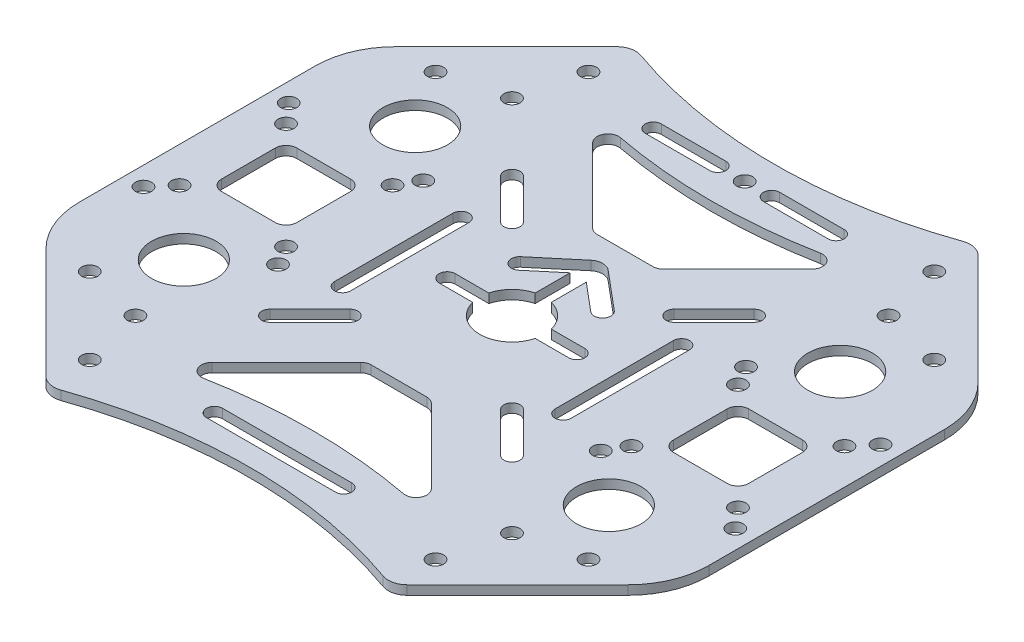
SolidWorks part; units mm, degrees
ref_plane "前基準面" through (0, 0, 0) normal (0, 0, 1) x (1, 0, 0)
ref_plane "上基準面" through (0, 0, 0) normal (0, 1, 0) x (1, 0, 0)
ref_plane "右基準面" through (0, 0, 0) normal (1, 0, 0) x (0, 0, -1)
sketch "草圖1" plane through (0, 0, 0) normal (0, 1, 0) x (1, 0, 0)
  line L0 (-88.3224, -92.0235) -> (-10.6127, -92.0235) construction
  line L1 (-96.5414, 45.9038) -> (-96.5414, -104.0962) construction
  line L2 (0, 5.7817) -> (0, -5.7817) construction
  line L3 (-13.0005, 0) -> (13.0005, 0) construction
  line L4 (-14.25, 25) -> (14.25, 25) construction
  line L5 (-14.25, 26.5) -> (14.25, 26.5)
  line L6 (-14.25, 23.5) -> (14.25, 23.5)
  line L7 (-14.25, -25) -> (14.25, -25) construction
  line L8 (-14.25, -26.5) -> (14.25, -26.5)
  line L9 (-14.25, -23.5) -> (14.25, -23.5)
  line L10 (-47.2341, 47.2341) -> (47.2341, -47.2341) construction
  line L11 (47.2341, 47.2341) -> (-47.2341, -47.2341) construction
  line L12 (-22.5, 22.5) -> (-15.0754, 15.0754) construction
  line L13 (-21.4393, 23.5607) -> (-14.0147, 16.136)
  line L14 (-23.5607, 21.4393) -> (-16.136, 14.0147)
  line L15 (22.5, 22.5) -> (15.0754, 15.0754) construction
  line L16 (21.4393, 23.5607) -> (14.0147, 16.136)
  line L17 (23.5607, 21.4393) -> (16.136, 14.0147)
  line L18 (22.5, -22.5) -> (15.0754, -15.0754) construction
  line L19 (21.4393, -23.5607) -> (14.0147, -16.136)
  line L20 (23.5607, -21.4393) -> (16.136, -14.0147)
  line L21 (-22.5, -22.5) -> (-15.0754, -15.0754) construction
  line L22 (-21.4393, -23.5607) -> (-14.0147, -16.136)
  line L23 (-23.5607, -21.4393) -> (-16.136, -14.0147)
  line L24 (-33.25, 22.4) -> (-33.25, -22.4) construction
  line L25 (-31.75, 22.4) -> (-31.75, -22.4)
  line L26 (-34.75, 22.4) -> (-34.75, -22.4)
  line L27 (-41.25, 23.25) -> (-41.25, -23.25) construction
  line L28 (-39.75, 23.25) -> (-39.75, -23.25)
  line L29 (-42.75, 23.25) -> (-42.75, -23.25)
  line L30 (-50.25, 25.2) -> (-50.25, -25.2) construction
  line L31 (-48.75, 25.2) -> (-48.75, -25.2)
  line L32 (-51.75, 25.2) -> (-51.75, -25.2)
  line L33 (50.25, 25.2) -> (50.25, -25.2) construction
  line L34 (48.75, 25.2) -> (48.75, -25.2)
  line L35 (51.75, 25.2) -> (51.75, -25.2)
  line L36 (41.25, 23.25) -> (41.25, -23.25) construction
  line L37 (39.75, 23.25) -> (39.75, -23.25)
  line L38 (42.75, 23.25) -> (42.75, -23.25)
  line L39 (33.25, 22.4) -> (33.25, -22.4) construction
  line L40 (31.75, 22.4) -> (31.75, -22.4)
  line L41 (34.75, 22.4) -> (34.75, -22.4)
  line L42 (-26, 14.3) -> (-26, -14.3) construction
  line L43 (-24.5, 14.3) -> (-24.5, -14.3)
  line L44 (-27.5, 14.3) -> (-27.5, -14.3)
  line L45 (-1.5, 5.8095) -> (-1.5, 12.3095)
  line L46 (-1.5, 12.3095) -> (-6.7013, 7.9451)
  line L47 (-8.6939, 10.3198) -> (-1.607, 16.2665)
  line L48 (8.6939, 10.3198) -> (1.607, 16.2665)
  line L49 (1.5, 5.8095) -> (1.5, 12.3095)
  line L50 (1.5, 12.3095) -> (6.7013, 7.9451)
  line L51 (26, 14.3) -> (26, -14.3) construction
  line L52 (24.5, 14.3) -> (24.5, -14.3)
  line L53 (27.5, 14.3) -> (27.5, -14.3)
  line L54 (-22.3, -33.3) -> (22.3, -33.3) construction
  line L55 (-22.3, -31.8) -> (22.3, -31.8)
  line L56 (-22.3, -34.8) -> (22.3, -34.8)
  line L57 (-31.9883, -54.6323) -> (-58.5, -28.1206)
  line L58 (-58.5, -28.1206) -> (-58.5, 28.1206)
  line L59 (31.9883, -54.6323) -> (58.5, -28.1206)
  line L60 (58.5, -28.1206) -> (58.5, 28.1206)
  line L61 (-31.9883, 54.6323) -> (-58.5, 28.1206)
  line L62 (31.9883, 54.6323) -> (58.5, 28.1206)
  line L63 (20.5663, -9.3678) -> (20.5663, 9.3678)
  line L64 (17.0742, 10.8143) -> (11.9044, 5.6446)
  line L65 (17.0742, -10.8143) -> (11.9044, -5.6446)
  line L66 (-17.0742, -10.8143) -> (-11.9044, -5.6446)
  line L67 (-17.0742, 10.8143) -> (-11.9044, 5.6446)
  line L68 (-20.5663, -9.3678) -> (-20.5663, 9.3678)
  line L69 (-22.2619, -40.2376) -> (22.2619, -40.2376)
  line L70 (22.2619, -40.2376) -> (24.4317, -42.4074)
  line L71 (-22.2619, -40.2376) -> (-24.4317, -42.4074)
  line L72 (32.138, 46.3508) -> (46.3508, 32.138) construction
  line L73 (3.7413, -66.2623) -> (66.2623, -3.7413) construction
  arc A0 (-14.25, 26.5) -> (-14.25, 23.5) centre (-14.25, 25) ccw
  arc A1 (14.25, 23.5) -> (14.25, 26.5) centre (14.25, 25) ccw
  arc A2 (-14.25, -26.5) -> (-14.25, -23.5) centre (-14.25, -25) cw
  arc A3 (14.25, -23.5) -> (14.25, -26.5) centre (14.25, -25) cw
  circle A4 centre (-35.0018, 35.0018) radius 1.5
  circle A5 centre (35.0018, -35.0018) radius 1.5
  circle A6 centre (-35.0018, -35.0018) radius 1.5
  circle A7 centre (35.0018, 35.0018) radius 1.5
  arc A8 (-21.4393, 23.5607) -> (-23.5607, 21.4393) centre (-22.5, 22.5) ccw
  arc A9 (-16.136, 14.0147) -> (-14.0147, 16.136) centre (-15.0754, 15.0754) ccw
  arc A10 (21.4393, 23.5607) -> (23.5607, 21.4393) centre (22.5, 22.5) cw
  arc A11 (16.136, 14.0147) -> (14.0147, 16.136) centre (15.0754, 15.0754) cw
  arc A12 (21.4393, -23.5607) -> (23.5607, -21.4393) centre (22.5, -22.5) ccw
  arc A13 (16.136, -14.0147) -> (14.0147, -16.136) centre (15.0754, -15.0754) ccw
  arc A14 (-21.4393, -23.5607) -> (-23.5607, -21.4393) centre (-22.5, -22.5) cw
  arc A15 (-16.136, -14.0147) -> (-14.0147, -16.136) centre (-15.0754, -15.0754) cw
  arc A16 (-31.75, 22.4) -> (-34.75, 22.4) centre (-33.25, 22.4) ccw
  arc A17 (-34.75, -22.4) -> (-31.75, -22.4) centre (-33.25, -22.4) ccw
  arc A18 (-39.75, 23.25) -> (-42.75, 23.25) centre (-41.25, 23.25) ccw
  arc A19 (-42.75, -23.25) -> (-39.75, -23.25) centre (-41.25, -23.25) ccw
  arc A20 (-48.75, 25.2) -> (-51.75, 25.2) centre (-50.25, 25.2) ccw
  arc A21 (-51.75, -25.2) -> (-48.75, -25.2) centre (-50.25, -25.2) ccw
  arc A22 (48.75, 25.2) -> (51.75, 25.2) centre (50.25, 25.2) cw
  arc A23 (51.75, -25.2) -> (48.75, -25.2) centre (50.25, -25.2) cw
  arc A24 (39.75, 23.25) -> (42.75, 23.25) centre (41.25, 23.25) cw
  arc A25 (42.75, -23.25) -> (39.75, -23.25) centre (41.25, -23.25) cw
  arc A26 (31.75, 22.4) -> (34.75, 22.4) centre (33.25, 22.4) cw
  arc A27 (34.75, -22.4) -> (31.75, -22.4) centre (33.25, -22.4) cw
  arc A28 (-24.5, 14.3) -> (-27.5, 14.3) centre (-26, 14.3) ccw
  arc A29 (-27.5, -14.3) -> (-24.5, -14.3) centre (-26, -14.3) ccw
  arc A30 (-1.5, 5.8095) -> (1.5, 5.8095) centre (0, 0) ccw
  arc A31 (-6.7013, 7.9451) -> (-8.6939, 10.3198) centre (-7.6976, 9.1325) cw
  arc A32 (-1.607, 16.2665) -> (1.607, 16.2665) centre (0, 14.3514) cw
  arc A33 (6.7013, 7.9451) -> (8.6939, 10.3198) centre (7.6976, 9.1325) ccw
  circle A34 centre (-32.138, -46.3508) radius 1.5
  circle A35 centre (-46.3508, -32.138) radius 1.5
  circle A36 centre (-32.138, 46.3508) radius 1.5
  circle A37 centre (-46.3508, 32.138) radius 1.5
  circle A38 centre (46.3508, 32.138) radius 1.5
  circle A39 centre (32.138, 46.3508) radius 1.5
  circle A40 centre (32.138, -46.3508) radius 1.5
  circle A41 centre (46.3508, -32.138) radius 1.5
  arc A42 (24.5, 14.3) -> (27.5, 14.3) centre (26, 14.3) cw
  arc A43 (27.5, -14.3) -> (24.5, -14.3) centre (26, -14.3) cw
  arc A44 (-22.3, -31.8) -> (-22.3, -34.8) centre (-22.3, -33.3) ccw
  arc A45 (22.3, -34.8) -> (22.3, -31.8) centre (22.3, -33.3) ccw
  arc A46 (-31.9883, -54.6323) -> (31.9883, -54.6323) centre (0, -138.7558) cw
  arc A47 (-31.9883, 54.6323) -> (31.9883, 54.6323) centre (0, 138.7558) ccw
  arc A48 (11.9044, -5.6446) -> (11.9044, 5.6446) centre (17.549, 0) cw
  arc A49 (20.5663, 9.3678) -> (17.0742, 10.8143) centre (18.5207, 9.3678) ccw
  arc A50 (20.5663, -9.3678) -> (17.0742, -10.8143) centre (18.5207, -9.3678) cw
  arc A51 (-20.5663, -9.3678) -> (-17.0742, -10.8143) centre (-18.5207, -9.3678) ccw
  arc A52 (-11.9044, -5.6446) -> (-11.9044, 5.6446) centre (-17.549, 0) ccw
  arc A53 (-20.5663, 9.3678) -> (-17.0742, 10.8143) centre (-18.5207, 9.3678) cw
  arc A54 (24.4317, -42.4074) -> (22.5661, -45.77) centre (23.0175, -43.8216) cw
  arc A55 (22.5661, -45.77) -> (0, -43.1906) centre (0, -143.1906) ccw
  arc A56 (-24.4317, -42.4074) -> (-22.5661, -45.77) centre (-23.0175, -43.8216) ccw
  arc A57 (-22.5661, -45.77) -> (0, -43.1906) centre (0, -143.1906) cw
  point P8 (0, 0)
  point P11 (0, 0)
  point P12 (0, 25)
  point P23 (0, -25)
  point P32 (0, 0)
  point P40 (-18.7877, 18.7877)
  point P48 (18.7877, 18.7877)
  point P55 (18.7877, -18.7877)
  point P62 (-18.7877, -18.7877)
  point P68 (-33.25, 0)
  point P74 (-41.25, 0)
  point P82 (-50.25, 0)
  point P88 (-26, 0)
  point P95 (50.25, 0)
  point P102 (41.25, 0)
  point P109 (33.25, 0)
  point P129 (0, -33.3)
  point P148 (0, 0)
  point P155 (26, 0)
  point P178 (-58.5, 0)
  point P179 (58.5, 0)
  point P182 (20.5663, 0)
  point P196 (-14.7218, -14.7218)
  point P203 (0, -40.2376)
  point P205 (35.0018, -35.0018)
  point P209 (-35.0018, 35.0018)
  dimension "D5" = 3
  dimension "D10" = 12
  dimension "D11" = 50
  dimension "D15" = 2.5
  dimension "D16" = 3
  dimension "D24" = 90
  dimension "D31" = 100
  dimension "D33" = 2
  dimension "D34" = 3
  dimension "D1" = 150
  dimension "D2" = 3
  dimension "D3" = 50
  dimension "D4" = 6
  dimension "D6" = 3
  dimension "D7" = 3
  dimension "D8" = 3
  dimension "D9" = 3
  dimension "D12" = 6.5
  dimension "D13" = 3
  dimension "D14" = 3.1
  dimension "D18" = 20.1
  dimension "D19" = 52
  dimension "D20" = 66.5
  dimension "D21" = 82.5
  dimension "D22" = 100.5
  dimension "D23" = 3
  dimension "D25" = 117
  dimension "D26" = 122.5
  dimension "D27" = 277.5115
  dimension "D28" = 10.5
  dimension "D29" = 45
  dimension "D30" = 33.3
  dimension "D32" = 45
  dimension "D35" = 99
  dimension "D36" = 46.5
  dimension "D37" = 28.6
  dimension "D38" = 44.8
  dimension "D39" = 50.4
  dimension "D40" = 28.5
  dimension "D41" = 44.6
  dimension "D42" = 9.3
  dimension "D17" = 4
extrude "填料-伸長1" add sketch "草圖1" along normal blind 1.7 contours L29 A19 L28 A18 | L26 A17 L25 A16 | A47 L61 L58 L57 A46 L59 L60 L62 A57 A56 L71 L69 L70 A54 A55 A45 L56 A44 L55 A41 A38 A37 A35 A34 A33 L50 L49 A30 L45 L46 A31 L47 A32 L48 A29 L44 A28 L43 A21 L32 A20 | L32 A21 L31 A20 | L44 A29 L43 A28 | A53 L68 A51 L66 A52 L67 | A50 L63 A49 L64 A48 L65 | A43 L53 A42 L52 | A27 L41 A26 L40 | A25 L38 A24 L37 | A23 L35 A22 L34 | A3 L9 A2 L8 | L56 A45 L55 A44 | A56 A57 A55 A54 L70 L69 L71 | L6 A1 L5 A0
fillet "圓角1" radius 3.5 4 edges at (-31.9883, 0.85, -54.6323) (31.9883, 0.85, -54.6323) (-31.9883, 0.85, 54.6323) (31.9883, 0.85, 54.6323)
fillet "圓角2" radius 15 4 edges at (-58.5, 0.85, 28.1206) (-58.5, 0.85, -28.1206) (58.5, 0.85, -28.1206) (58.5, 0.85, 28.1206)
sketch "草圖2" plane through (0, 1.7, 0) normal (0, 1, 0) x (1, 0, 0)
  line L0 (-93.5709, 0) -> (93.5709, 0) construction
  line L1 (335.0389, 1531.6906) -> (1989.0389, 1531.9793) construction
  line L2 (37, -7) -> (47, -7)
  line L3 (0, 61.188) -> (0, -61.188) construction
  line L4 (35, -5) -> (35, 5)
  line L5 (37, 7) -> (47, 7)
  line L6 (49, -5) -> (49, 5)
  line L7 (35, -7) -> (49, 7) construction
  line L8 (35, 7) -> (49, -7) construction
  line L9 (-37, 7) -> (-47, 7)
  line L10 (-49, -5) -> (-49, 5)
  line L11 (-35, 7) -> (-49, -7) construction
  line L12 (-35, -5) -> (-35, 5)
  line L13 (-35, -7) -> (-49, 7) construction
  line L14 (-37, -7) -> (-47, -7)
  line L15 (-50.0285, -50.0285) -> (54.0325, 54.0325) construction
  line L16 (48.9236, -48.9236) -> (-55.1374, 55.1374) construction
  line L17 (-12.05, 0) -> (12.05, 0) construction
  line L18 (-12.05, 1.5) -> (12.05, 1.5)
  line L19 (-12.05, -1.5) -> (12.05, -1.5)
  line L20 (-20.5, 11) -> (-20.5, -11) construction
  line L21 (-19, 11) -> (-19, -11)
  line L22 (-22, 11) -> (-22, -11)
  line L23 (20.5, 11) -> (20.5, -11) construction
  line L24 (19, 11) -> (19, -11)
  line L25 (22, 11) -> (22, -11)
  line L26 (-12, -43.3) -> (12, -43.3) construction
  line L27 (-12, -41.8) -> (12, -41.8)
  line L28 (-12, -44.8) -> (12, -44.8)
  line L29 (5, 43.25) -> (17, 43.25) construction
  line L30 (5, 44.75) -> (17, 44.75)
  line L31 (5, 41.75) -> (17, 41.75)
  line L32 (-5, 43.25) -> (-17, 43.25) construction
  line L33 (-5, 44.75) -> (-17, 44.75)
  line L34 (-5, 41.75) -> (-17, 41.75)
  line L35 (-42, -13.5) -> (-42, 13.5) construction
  line L36 (-6.5858, -21.5858) -> (-20.3609, -35.3609)
  line L37 (-5.1716, -21) -> (5.1716, -21)
  line L38 (6.5858, -21.5858) -> (20.3609, -35.3609)
  line L39 (-5.1716, 21) -> (5.1716, 21)
  line L40 (-6.5858, 21.5858) -> (-20.3609, 35.3609)
  line L41 (6.5858, 21.5858) -> (20.3609, 35.3609)
  circle A0 centre (0, 43.25) radius 1.5
  arc A1 (-12.05, 1.5) -> (-12.05, -1.5) centre (-12.05, 0) ccw
  arc A2 (12.05, -1.5) -> (12.05, 1.5) centre (12.05, 0) ccw
  arc A3 (-19, 11) -> (-22, 11) centre (-20.5, 11) ccw
  arc A4 (-22, -11) -> (-19, -11) centre (-20.5, -11) ccw
  arc A5 (19, 11) -> (22, 11) centre (20.5, 11) cw
  arc A6 (22, -11) -> (19, -11) centre (20.5, -11) cw
  circle A7 centre (39.5, 21.5) radius 6
  circle A8 centre (39.5, -21.5) radius 6
  circle A9 centre (-39.5, -21.5) radius 6
  circle A10 centre (-39.5, 21.5) radius 6
  arc A11 (-12, -41.8) -> (-12, -44.8) centre (-12, -43.3) ccw
  arc A12 (12, -44.8) -> (12, -41.8) centre (12, -43.3) ccw
  arc A13 (5, 44.75) -> (5, 41.75) centre (5, 43.25) ccw
  arc A14 (17, 41.75) -> (17, 44.75) centre (17, 43.25) ccw
  arc A15 (-5, 44.75) -> (-5, 41.75) centre (-5, 43.25) cw
  arc A16 (-17, 41.75) -> (-17, 44.75) centre (-17, 43.25) cw
  arc A17 (-37, 7) -> (-35, 5) centre (-37, 5) cw
  arc A18 (-47, 7) -> (-49, 5) centre (-47, 5) ccw
  arc A19 (-49, -5) -> (-47, -7) centre (-47, -5) ccw
  arc A20 (-37, -7) -> (-35, -5) centre (-37, -5) ccw
  arc A21 (49, 5) -> (47, 7) centre (47, 5) ccw
  arc A22 (35, 5) -> (37, 7) centre (37, 5) cw
  arc A23 (35, -5) -> (37, -7) centre (37, -5) ccw
  arc A24 (47, -7) -> (49, -5) centre (47, -5) ccw
  circle A25 centre (-32.1005, 9.8995) radius 1.5
  circle A26 centre (-32.1005, -9.8995) radius 1.5
  circle A27 centre (-51.8995, 9.8995) radius 1.5
  circle A28 centre (-51.8995, -9.8995) radius 1.5
  circle A29 centre (-55, 13.5) radius 1.5
  circle A30 centre (-55, -13.5) radius 1.5
  circle A31 centre (-30, 13.5) radius 1.5
  circle A32 centre (-30, -13.5) radius 1.5
  circle A33 centre (55, -13.5) radius 1.5
  circle A34 centre (51.8995, -9.8995) radius 1.5
  circle A35 centre (55, 13.5) radius 1.5
  circle A36 centre (51.8995, 9.8995) radius 1.5
  circle A37 centre (30, 13.5) radius 1.5
  circle A38 centre (32.1005, 9.8995) radius 1.5
  circle A39 centre (30, -13.5) radius 1.5
  circle A40 centre (32.1005, -9.8995) radius 1.5
  arc A41 (-18.5752, -38.7403) -> (18.5752, -38.7403) centre (0, -137) cw
  arc A42 (-18.5752, 38.7403) -> (18.5752, 38.7403) centre (0, 137) ccw
  arc A43 (-20.3609, 35.3609) -> (-18.5752, 38.7403) centre (-18.9467, 36.7751) cw
  arc A44 (18.5752, 38.7403) -> (20.3609, 35.3609) centre (18.9467, 36.7751) cw
  arc A45 (5.1716, 21) -> (6.5858, 21.5858) centre (5.1716, 23) ccw
  arc A46 (-5.1716, 21) -> (-6.5858, 21.5858) centre (-5.1716, 23) cw
  arc A47 (18.5752, -38.7403) -> (20.3609, -35.3609) centre (18.9467, -36.7751) ccw
  arc A48 (-18.5752, -38.7403) -> (-20.3609, -35.3609) centre (-18.9467, -36.7751) cw
  arc A49 (-6.5858, -21.5858) -> (-5.1716, -21) centre (-5.1716, -23) cw
  arc A50 (6.5858, -21.5858) -> (5.1716, -21) centre (5.1716, -23) ccw
  point P0 (42, 0)
  point P4 (0, 0)
  point P9 (0, 0)
  point P20 (-42, 0)
  point P24 (0, 0)
  point P27 (0, 0)
  point P34 (-20.5, 0)
  point P43 (20.5, 0)
  point P56 (0, -43.3)
  point P64 (11, 43.25)
  point P72 (-11, 43.25)
  point P119 (-42, 0)
  point P144 (0, -21)
  point P155 (-25.2369, 40.2369)
  point P158 (25.2369, 40.2369)
  point P161 (6, 21)
  point P164 (-6, 21)
  point P167 (25.2369, -40.2369)
  point P170 (-25.2369, -40.2369)
  point P173 (-6, -21)
  point P176 (6, -21)
  dimension "D2" = 3
  dimension "D10" = 12
  dimension "D19" = 2
  dimension "D20" = 3
  dimension "D22" = 100
  dimension "D27" = 2
  dimension "D1" = 14
  dimension "D3" = 84
  dimension "D4" = 90
  dimension "D5" = 3
  dimension "D6" = 24.1
  dimension "D7" = 3
  dimension "D8" = 41
  dimension "D9" = 22
  dimension "D11" = 43
  dimension "D12" = 79
  dimension "D13" = 3
  dimension "D14" = 24
  dimension "D15" = 43.3
  dimension "D16" = 22
  dimension "D17" = 12
  dimension "D18" = 43.25
  dimension "D21" = 27
  dimension "D23" = 90
  dimension "D24" = 12
  dimension "D25" = 42
  dimension "D26" = 274
  dimension "D28" = 25
  dimension "D29" = 14
  dimension "D30" = 12
extrude "除料-伸長1" cut sketch "草圖2" against normal through all
